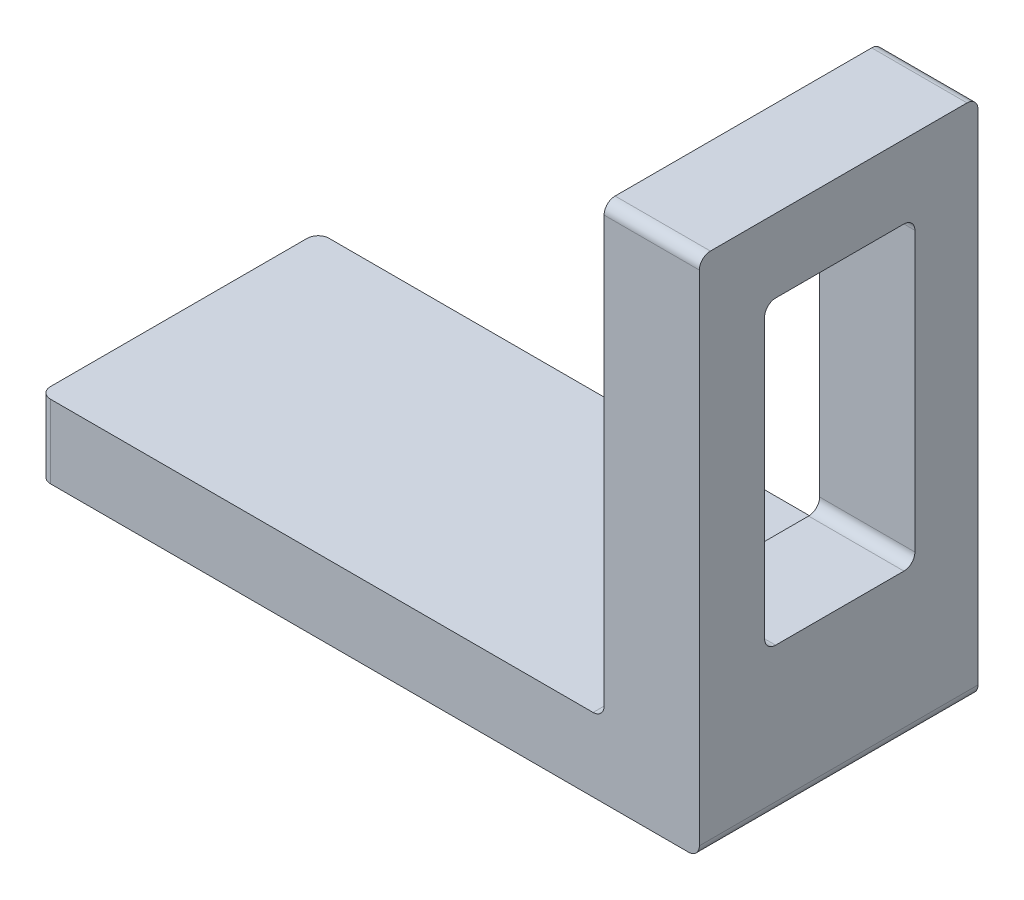
SolidWorks part; units mm, degrees
ref_plane "Front Plane" through (0, 0, 0) normal (0, 0, 1) x (1, 0, 0)
ref_plane "Top Plane" through (0, 0, 0) normal (0, 1, 0) x (1, 0, 0)
ref_plane "Right Plane" through (0, 0, 0) normal (1, 0, 0) x (0, 0, -1)
sketch "Sketch1" plane through (0, 0, 0) normal (0, 0, 1) x (1, 0, 0)
  line L0 (0, 0) -> (90, 0)
  line L1 (90, 0) -> (90, 71)
  line L2 (90, 71) -> (77, 71)
  line L3 (77, 71) -> (77, 10)
  line L4 (77, 10) -> (0, 10)
  line L5 (0, 10) -> (0, 0)
  dimension "D1" = 90
  dimension "D2" = 61
  dimension "D3" = 13
  dimension "D4" = 10
extrude "Boss-Extrude1" add sketch "Sketch1" along normal blind 38
sketch "Sketch3" plane through (0, 0, 0) normal (0, -1, 0) x (1, 0, 0)
  line L0 (0, 19) -> (34.1, 19)
  line L1 (0, 38) -> (0, 0) construction
  circle A0 centre (34.1, 19) radius 10.5
  circle A1 centre (23.6, 19) radius 1.4
  circle A2 centre (34.1, 29.5) radius 1.4
  circle A3 centre (44.6, 19) radius 1.4
  circle A4 centre (34.1, 8.5) radius 1.4
  point P13 (0, 19)
  dimension "D2" = 21
  dimension "D3" = 2.8
  dimension "D4" = 2.8
  dimension "D5" = 2.8
  dimension "D6" = 2.8
  dimension "D1" = 34.1
extrude "Cut-Extrude2" cut sketch "Sketch3" against normal blind 8 contours A1 | A4 | A3 | A2
sketch "Sketch4" plane through (77, 0, 0) normal (-1, 0, 0) x (0, 0, 1)
  line L0 (38, 71) -> (0, 71) construction
  line L1 (8.6048, 61) -> (29.1048, 61)
  line L2 (8.6048, 61) -> (8.6048, 20)
  line L3 (8.6048, 20) -> (29.1048, 20)
  line L4 (29.1048, 61) -> (29.1048, 20)
  line L5 (38, 10) -> (0, 10) construction
  dimension "D1" = 10
  dimension "D2" = 10
  dimension "D3" = 41
  dimension "D4" = 20.5
extrude "Cut-Extrude4" cut sketch "Sketch4" against normal through all contours L1 L4 L3 L2
sketch "Sketch7" plane through (77, 0, 0) normal (-1, 0, 0) x (0, 0, 1)
  circle A0 centre (13.9066, 65.016) radius 1.4
  circle A1 centre (23.8066, 65.016) radius 1.4
  circle A2 centre (13.9066, 16.416) radius 1.4
  circle A3 centre (23.8066, 16.416) radius 1.4
  point P0 (0, 0)
  dimension "D4" = 2.8
  dimension "D5" = 2.8
  dimension "D6" = 2.8
  dimension "D7" = 2.8
  dimension "D1" = 48.6
  dimension "D2" = 9.9
  dimension "D3" = 9.9
extrude "Cut-Extrude6" cut sketch "Sketch7" against normal blind 8
fillet "Fillet1" radius 1.5 4 edges at (83.5, 61, 29.1048) (83.5, 61, 8.6048) (83.5, 20, 29.1048) (83.5, 20, 8.6048)
fillet "Fillet2" radius 1.5 6 edges at (0, 5, 0) (0, 5, 38) (77, 10, 19) (90, 0, 19) (83.5, 71, 0) (83.5, 71, 38)
